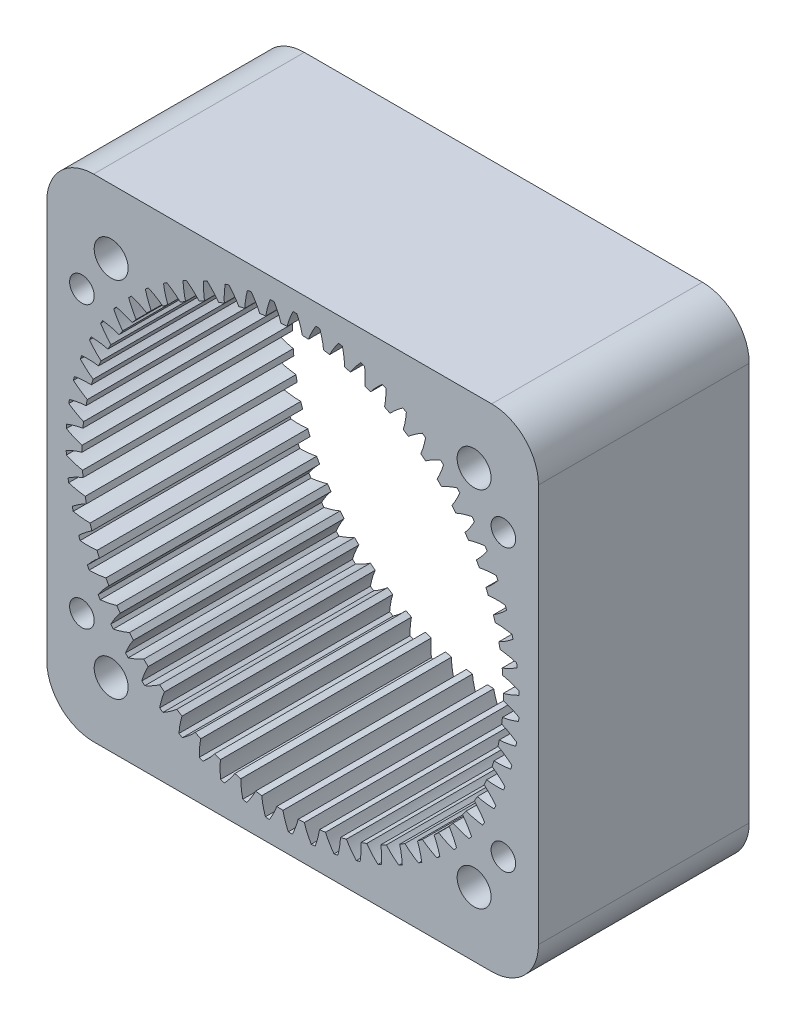
SolidWorks part; units mm, degrees
other "标注1"
sketch "草图9" plane through (-21, -21, 36) normal (-0.2153, -0.0648, 0.9744) x (0.3119, -0.9501, 0.0057)
other "标注2"
sketch "草图20" plane through (-30, -30, 20) normal (-0.0347, -0.0183, 0.9992) x (0.9994, -0.0065, 0.0346)
other "标注3"
sketch "草图27" plane through (-23.5298, 22.2328, 18) normal (-0.0197, 0.0107, 0.9997) x (0.9998, 0.0061, 0.0196)
ref_plane "前视基准面" through (0, 0, 0) normal (0, 0, 1) x (1, 0, 0)
ref_plane "上视基准面" through (0, 0, 0) normal (0, 1, 0) x (1, 0, 0)
ref_plane "右视基准面" through (0, 0, 0) normal (1, 0, 0) x (0, 0, -1)
sketch "草图1" plane through (0, 0, 0) normal (0, 0, 1) x (1, 0, 0)
  line L5 (-17.2128, -17.2128) -> (24.7872, 24.7872) construction
  line L6 (-21, 21) -> (21, -21) construction
  line L7 (21, 21) -> (-21, 21)
  line L8 (21, 21) -> (21, -21)
  line L9 (21, -21) -> (-21, -21)
  line L10 (-21, 21) -> (-21, -21)
  line L11 (0, -21) -> (0, 21) construction
  line L12 (21, 0) -> (-21, 0) construction
  circle A9 centre (0, 0) radius 30 construction
  circle A30 centre (15.5, 15.5) radius 1.55 construction
  circle A31 centre (15.5, -15.5) radius 1.55 construction
  circle A32 centre (-15.5, -15.5) radius 1.55 construction
  circle A33 centre (-15.5, 15.5) radius 1.55 construction
  point P31 (0, 0)
  point P37 (0, 0)
  point P48 (0, 0)
  dimension "D1" = 42
  dimension "D4" = 60
  dimension "D6" = 42
  dimension "D2" = 15.5
  dimension "D3" = 15.5
  dimension "D9" = 3.1
  dimension "D10" = 4
extrude "凸台-拉伸1" add sketch "草图1" along normal blind 18 contours L7 L10 L9 L8 A33 A32 A31 A30
sketch "草图6" plane through (0, 0, 0) normal (0, 0, 1) x (1, 0, 0)
  line L0 (0, 0) -> (17.4783, 0) construction
  line L1 (0, 0) -> (35.0568, 1.4114) construction
  line L2 (0, 0) -> (18.5979, 0.2772) construction
  circle A0 centre (0, 0) radius 18.6 construction
  circle A1 centre (0, 0) radius 5 construction
  circle A2 centre (0, 0) radius 17.4783 construction
  circle A3 centre (0, 0) radius 19.35 construction
  arc A4 (18.3136, -3.2516) -> (18.5979, 0.2772) centre (0, 0) cw construction
  circle A5 centre (0, 0) radius 10
  circle A7 centre (0, 0) radius 18
  arc A8 (19.3266, 0.951) -> (19.3404, 0.6105) centre (0, 0) cw
  spline S0 degree 4 poles (17.4783, 0) (17.4925, 0.0003) (17.5322, 0.0022) (17.607, 0.0095) (17.7287, 0.0269) (17.9531, 0.0708) (18.219, 0.1425) (18.5148, 0.2419) (18.8271, 0.3668) (19.0904, 0.4849) (19.3492, 0.6127) (19.6033, 0.7493) (19.9061, 0.9251) (20.2627, 1.1511) (20.668, 1.4349) (21.1151, 1.7826) (21.5533, 2.1589) (21.9735, 2.5535) (22.3775, 2.9674) (22.7628, 3.3942) (23.1343, 3.8408) (23.4399, 4.2347) (23.6995, 4.5935) (23.8967, 4.8761) (24.0713, 5.1411) (24.2387, 5.3961) (24.5035, 5.8331) (24.6633, 6.1083) (24.9023, 6.5423) (24.9838, 6.7039) (25.0508, 6.8322) knots 0 0 0 0 0 0.005377 0.015084 0.028532 0.04661 0.092111 0.119476 0.146842 0.174209 0.201575 0.228941 0.256307 0.307035 0.361767 0.4165 0.471232 0.525964 0.580697 0.635429 0.690161 0.744894 0.77226 0.799626 0.826992 0.854358 0.909091 0.954545 1 1 1 1 1 construction
  spline S1 degree 4 poles (17.4783, 0) (17.4925, 0.0003) (17.5322, 0.0022) (17.607, 0.0095) (17.7287, 0.0269) (17.9531, 0.0708) (18.219, 0.1425) (18.5148, 0.2419) (18.8271, 0.3668) (19.0904, 0.4849) (19.3492, 0.6127) (19.6033, 0.7493) (19.9061, 0.9251) (20.2627, 1.1511) (20.668, 1.4349) (21.1151, 1.7826) (21.5533, 2.1589) (21.9735, 2.5535) (22.3775, 2.9674) (22.7628, 3.3942) (23.1343, 3.8408) (23.4399, 4.2347) (23.6995, 4.5935) (23.8967, 4.8761) (24.0713, 5.1411) (24.2387, 5.3961) (24.4258, 5.7049) (24.5246, 5.8715) (24.5902, 5.985) knots 0 0 0 0 0 0.005377 0.015084 0.028532 0.04661 0.092111 0.119476 0.146842 0.174209 0.201575 0.228941 0.256307 0.307035 0.361767 0.4165 0.471232 0.525964 0.580697 0.635429 0.690161 0.744894 0.77226 0.799626 0.826992 0.854358 0.909091 0.909091 0.909091 0.909091 0.909091
  spline S2 degree 4 poles (17.2013, 1.4625) (17.2171, 1.4634) (17.2615, 1.4649) (17.3455, 1.4635) (17.4824, 1.4551) (17.7362, 1.4264) (18.0386, 1.3704) (18.3767, 1.2863) (18.7356, 1.1753) (19.0393, 1.0676) (19.3387, 0.9485) (19.6338, 0.8192) (19.9867, 0.6508) (20.4039, 0.4312) (20.8804, 0.1518) (21.4093, -0.1951) (21.9308, -0.5747) (22.4339, -0.9761) (22.9208, -1.4006) (23.388, -1.841) (23.8416, -2.3047) (24.2171, -2.7157) (24.5382, -3.0918) (24.7831, -3.3886) (25.0013, -3.6679) (25.2104, -3.9367) (25.4464, -4.2636) (25.5714, -4.4402) (25.6545, -4.5607) knots 0 0 0 0 0 0.005377 0.015084 0.028532 0.04661 0.092111 0.119476 0.146842 0.174209 0.201575 0.228941 0.256307 0.307035 0.361767 0.4165 0.471232 0.525964 0.580697 0.635429 0.690161 0.744894 0.77226 0.799626 0.826992 0.854358 0.909091 0.909091 0.909091 0.909091 0.909091
  point P6 (30.6834, 1.2647)
  dimension "D1" = 37.2
  dimension "D2" = 10
  dimension "D3" = 38.7
  dimension "D4" = 34.9566
  dimension "D6" = 36
  dimension "D7" = 20
  dimension "D5" = 1.452
extrude "切除-拉伸1" cut sketch "草图6" along normal through all
pattern_circular "阵列(圆周)1" count 62 over 360 about axis through (0, 0, 0) along (0, 0, -1) of "切除-拉伸1"
fillet "圆角2" radius 4 4 edges at (21, -21, 9) (-21, -21, 9) (-21, 21, 9) (21, 21, 9)
sketch "草图23" plane through (0, 0, 0) normal (0, 0, -1) x (-1, 0, 0)
  line L0 (-21, 17) -> (-21, -17) construction
  line L1 (-21, 13) -> (-17, 13)
  line L2 (-21, 13) -> (-21, 9)
  line L5 (-17, 21) -> (17, 21) construction
  line L18 (-21, 9) -> (-17, 13)
  line L19 (9, 21) -> (13, 17)
  line L20 (13, 21) -> (13, 17)
  line L21 (13, 21) -> (9, 21)
  line L22 (21, -9) -> (17, -13)
  line L23 (21, -13) -> (17, -13)
  line L24 (21, -13) -> (21, -9)
  line L25 (-9, -21) -> (-13, -17)
  line L26 (-13, -21) -> (-13, -17)
  line L27 (-13, -21) -> (-9, -21)
  point P19 (0, 0)
  point P23 (-7, 0)
  dimension "D1" = 4
  dimension "D2" = 4
  dimension "D3" = 8
  dimension "D4" = 4
extrude "切除-拉伸14" [suppressed] cut sketch "草图23" against normal blind 3
sketch "草图24" plane through (0, 0, 18) normal (0, 0, 1) x (1, 0, 0)
  line L0 (-21, 13) -> (-17, 13)
  line L1 (-21, 13) -> (-21, 9)
  line L16 (-21, 17) -> (-21, -17) construction
  line L17 (17, 21) -> (-17, 21) construction
  line L30 (-21, 9) -> (-17, 13)
  line L40 (9, 21) -> (13, 17)
  line L41 (13, 21) -> (13, 17)
  line L42 (13, 21) -> (9, 21)
  line L43 (21, -9) -> (17, -13)
  line L44 (21, -13) -> (17, -13)
  line L45 (21, -13) -> (21, -9)
  line L46 (-9, -21) -> (-13, -17)
  line L47 (-13, -21) -> (-13, -17)
  line L48 (-13, -21) -> (-9, -21)
  point P16 (0.2043, -0.1277)
  point P20 (0.2043, -0.1277)
  point P21 (0, 0)
  point P24 (-7, 0)
  dimension "D1" = 4
  dimension "D2" = 4
  dimension "D3" = 8
  dimension "D4" = 4
extrude "切除-拉伸15" [suppressed] cut sketch "草图24" against normal blind 4
sketch "草图25" plane through (0, 0, 18) normal (0, 0, 1) x (1, 0, 0)
  line L0 (17, 21) -> (-17, 21) construction
  line L1 (-21, 17) -> (-21, -17) construction
  line L2 (0, 22.2328) -> (0, -23.0812) construction
  line L3 (-23.5298, 0) -> (36.1925, 0) construction
  circle A0 centre (-18, 12) radius 1.05
  circle A1 centre (18, 12) radius 1.05
  circle A2 centre (18, -12) radius 1.05
  circle A3 centre (-18, -12) radius 1.05
  dimension "D1" = 2.1
  dimension "D2" = 9
  dimension "D3" = 3
extrude "切除-拉伸16" cut sketch "草图25" against normal through all
sketch "草图28" plane through (0, 0, 18) normal (0, 0, 1) x (1, 0, 0)
  line L0 (-23.5298, 0) -> (36.1925, 0) construction
  line L1 (0, 22.2328) -> (0, -23.0812) construction
  circle A0 centre (-15.5, 15.5) radius 1.45
  circle A1 centre (15.5, 15.5) radius 1.45
  circle A2 centre (15.5, -15.5) radius 1.45
  circle A3 centre (-15.5, -15.5) radius 1.45
  point P15 (0, 0)
  dimension "D1" = 2.9
  dimension "D2" = 15.5
  dimension "D3" = 15.5
  dimension "D4" = 4
extrude "切除-拉伸17" cut sketch "草图28" against normal blind 8
sketch "草图29" plane through (0, 0, 0) normal (0, 0, -1) x (-1, 0, 0)
  line L2 (-16.9706, 16.9706) -> (0, 0) construction
  line L3 (0, 22.2328) -> (0, -23.0812) construction
  circle A0 centre (-16.9706, 16.9706) radius 2.1
  circle A1 centre (16.9706, 16.9706) radius 2.1
  circle A2 centre (16.9706, -16.9706) radius 2.1
  circle A3 centre (-16.9706, -16.9706) radius 2.1
  point P12 (0, 0)
  dimension "D4" = 4.2
  dimension "D1" = 24
  dimension "D3" = 45
  dimension "D2" = 4
extrude "切除-拉伸18" cut sketch "草图29" against normal blind 8
equation "\"m\"= 0.6"
equation "\"z\"= 62"
equation "\"a\"= 20"
equation "\"d\"= \"m\" * \"z\""
equation "\"da\"= \"m\" * ( \"z\" - 2 )"
equation "\"df\"= \"d\" + 2.5 * \"m\""
equation "\"db\"= \"d\" * cos ( \"a\" )"
equation "\"s\"= pi * \"m\" / 2"
equation "\"D1@草图6\"=\"d\""
equation "\"D3@草图6\"=\"df\""
equation "\"D4@草图6\"=\"db\""
equation "\"D6@草图6\"=\"da\""
equation "\"sr\"= 360 / \"z\" / 4"
equation "\"D5@草图6\"=\"sr\""
equation "\"D1@阵列(圆周)1\"=\"z\""
